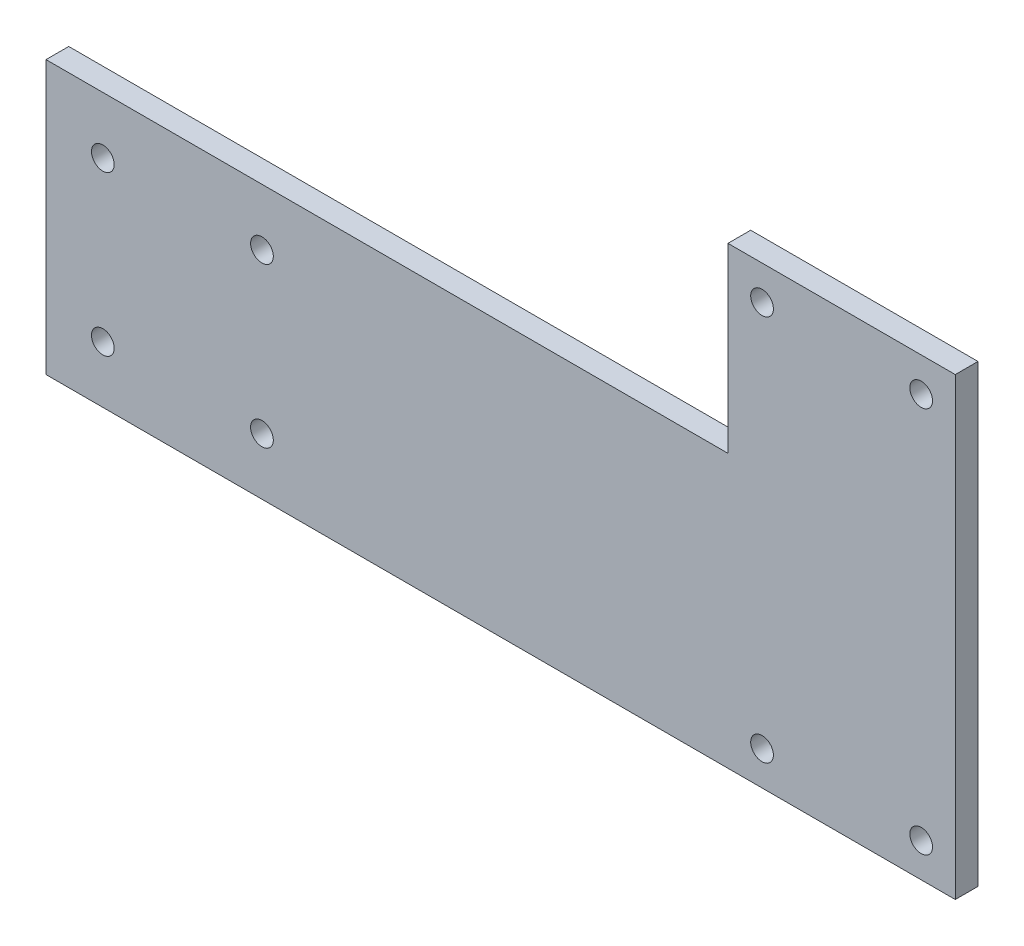
SolidWorks part; units mm, degrees
material "5052-H32"
ref_plane "Front Plane" through (0, 0, 0) normal (0, 0, 1) x (1, 0, 0)
ref_plane "Top Plane" through (0, 0, 0) normal (0, 1, 0) x (1, 0, 0)
ref_plane "Right Plane" through (0, 0, 0) normal (1, 0, 0) x (0, 0, -1)
sketch "Sketch1" plane through (0, 0, 0) normal (0, 0, 1) x (1, 0, 0)
  line L0 (0, 89.655) -> (0, -80.6595) construction
  line L1 (-100, 50) -> (100, 50)
  line L2 (-100, 50) -> (-100, -50)
  line L3 (-100, -50) -> (100, -50)
  line L4 (100, 50) -> (100, -50)
  line L5 (-100, 50) -> (100, -50) construction
  line L6 (-100, -50) -> (100, 50) construction
  line L7 (-119.1901, 0) -> (154.2728, 0) construction
  circle A8 centre (-92.5, 42.5) radius 2.5
  circle A9 centre (-57.5, 42.5) radius 2.5
  circle A12 centre (57.5, -42.5) radius 2.5
  circle A13 centre (92.5, -42.5) radius 2.5
  circle A14 centre (57.5, 42.5) radius 2.5
  circle A15 centre (92.5, 42.5) radius 2.5
  circle A16 centre (-92.5, -42.5) radius 2.5 [skipped]
  circle A17 centre (-57.5, -42.5) radius 2.5 [skipped]
  circle A18 centre (-87.5, -37.5) radius 2.5
  circle A19 centre (-52.5, -37.5) radius 2.5
  point P0 (0, 0)
  dimension "D3" = 5
  dimension "D4" = 5
  dimension "D11" = 5
  dimension "D12" = 5
  dimension "D13" = 12.5
  dimension "D1" = 200
  dimension "D2" = 100
  dimension "D5" = 7.5
  dimension "D6" = 7.5
  dimension "D7" = 7.5
  dimension "D8" = 42.5
  dimension "D14" = 12.5
  dimension "D15" = 12.5
  dimension "D16" = 35
  dimension "D9" = 2
  dimension "D10" = 2
extrude "Boss-Extrude1" add sketch "Sketch1" along normal blind 5
sketch "Sketch2" plane through (0, 0, 5) normal (0, 0, 1) x (1, 0, 0)
  line L2 (-100, 50) -> (-100, -50) construction
  circle A2 centre (-87.5, -2.5) radius 2.5
  circle A3 centre (-52.5, -2.5) radius 2.5
  circle A4 centre (-87.5, -37.5) radius 2.5
  circle A5 centre (-52.5, -37.5) radius 2.5
  dimension "D1" = 5
  dimension "D2" = 5
  dimension "D3" = 35
  dimension "D4" = 35
  dimension "D5" = 12.5
  dimension "D6" = 35
extrude "Cut-Extrude1" cut sketch "Sketch2" against normal blind 5
sketch "Sketch4" plane through (0, 0, 5) normal (0, 0, 1) x (1, 0, 0)
  line L0 (50, 50) -> (50, 10)
  line L1 (100, 50) -> (-100, 50) construction
  line L2 (50, 10) -> (-100, 10)
  line L3 (-100, 50) -> (-100, -50) construction
  line L4 (-100, 10) -> (-100, 50)
  line L5 (-100, 50) -> (50, 50)
  line L6 (100, -50) -> (100, 50) construction
  dimension "D1" = 50
  dimension "D2" = 40
extrude "Cut-Extrude3" cut sketch "Sketch4" against normal blind 30
